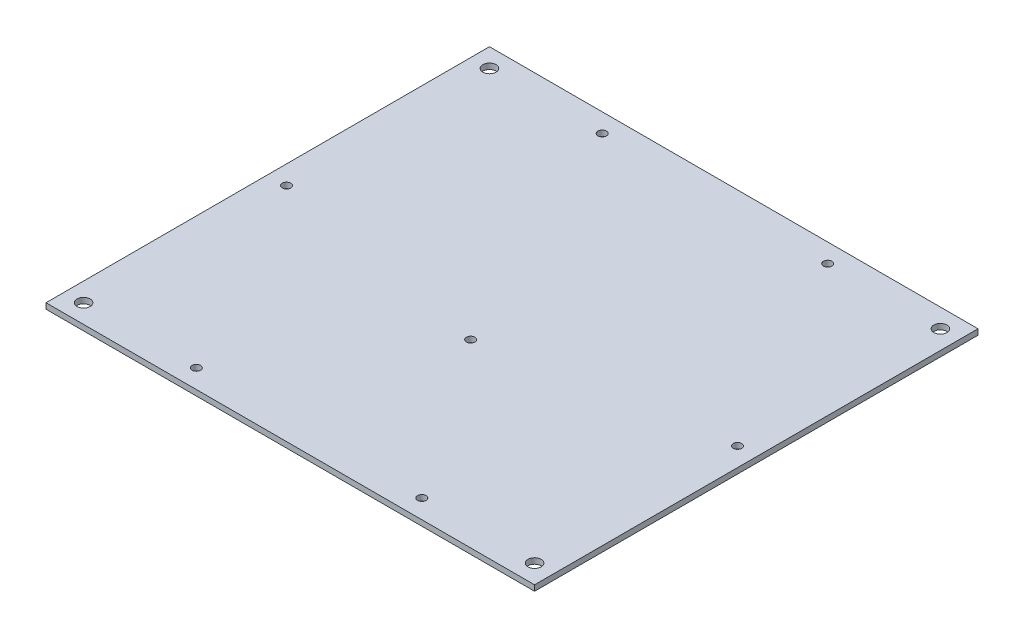
SolidWorks part; units mm, degrees
ref_plane "Спереди" through (0, 0, 0) normal (0, 0, 1) x (1, 0, 0)
ref_plane "Сверху" through (0, 0, 0) normal (0, 1, 0) x (1, 0, 0)
ref_plane "Справа" through (0, 0, 0) normal (1, 0, 0) x (0, 0, -1)
sketch "Эскиз1" plane through (0, 0, 0) normal (0, 1, 0) x (1, 0, 0)
  line L0 (0, 0) -> (260, 0)
  line L1 (0, 0) -> (0, 236)
  line L2 (260, 0) -> (260, 236)
  line L3 (0, 236) -> (260, 236)
  line L4 (10, 226) -> (250, 226) construction
  line L5 (10, 226) -> (10, 10) construction
  line L6 (250, 226) -> (250, 10) construction
  line L7 (10, 10) -> (250, 10) construction
  line L8 (70, 226) -> (70, 10) construction
  line L9 (190, 226) -> (190, 10) construction
  circle A0 centre (10, 118) radius 2.25
  circle A1 centre (250, 118) radius 2.25
  circle A2 centre (70, 226) radius 2.25
  circle A3 centre (190, 226) radius 2.25
  circle A4 centre (70, 10) radius 2.25
  circle A5 centre (190, 10) radius 2.25
  circle A6 centre (10, 226) radius 3.5
  circle A7 centre (250, 226) radius 3.5
  circle A8 centre (250, 10) radius 3.5
  circle A9 centre (10, 10) radius 3.5
  dimension "D7" = 4.5
  dimension "D8" = 4.5
  dimension "D11" = 4.5
  dimension "D12" = 4.5
  dimension "D13" = 4.5
  dimension "D14" = 4.5
  dimension "D15" = 7
  dimension "D16" = 7
  dimension "D17" = 7
  dimension "D18" = 7
  dimension "D1" = 236
  dimension "D2" = 260
  dimension "D3" = 10
  dimension "D4" = 10
  dimension "D5" = 10
  dimension "D6" = 10
  dimension "D9" = 70
  dimension "D10" = 70
extrude "Бобышка-Вытянуть1" add sketch "Эскиз1" along normal blind 3
sketch "Sketch1" plane through (0, 3, 0) normal (0, 1, 0) x (1, 0, 0)
  line L0 (240, 86) -> (20, 86) construction
  line L1 (240, 86) -> (20, 86) construction
  line L2 (130, 86) -> (130, 96) construction
  circle A0 centre (130, 96) radius 2.25
  dimension "D2" = 4.5
  dimension "D1" = 10
extrude "Cut-Extrude1" cut sketch "Sketch1" against normal through all
